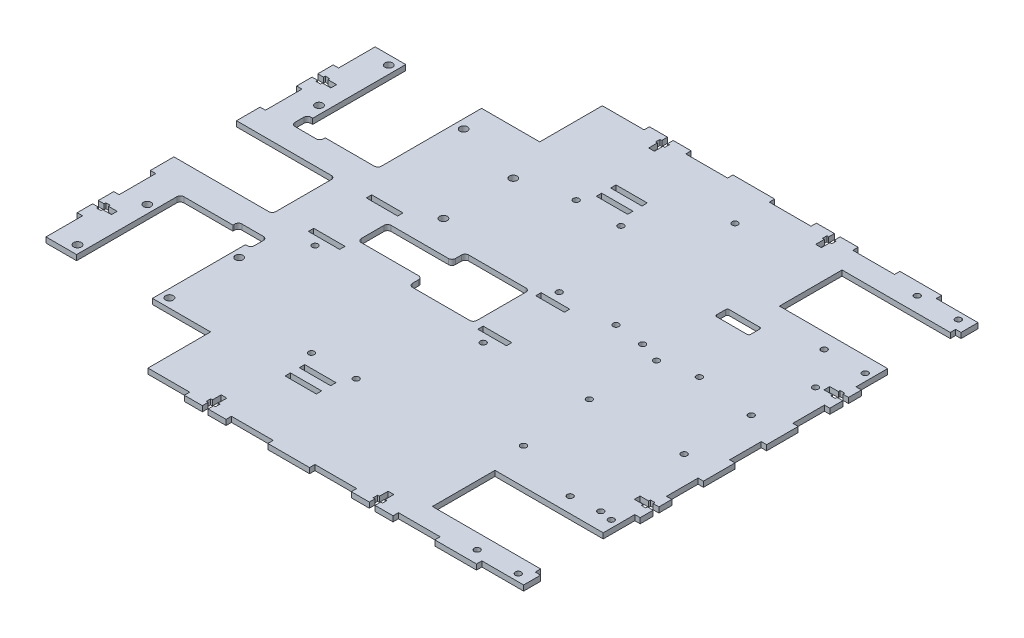
SolidWorks part; units mm, degrees
ref_plane "Front Plane" through (0, 0, 0) normal (0, 0, 1) x (1, 0, 0)
ref_plane "Top Plane" through (0, 0, 0) normal (0, 1, 0) x (1, 0, 0)
ref_plane "Right Plane" through (0, 0, 0) normal (1, 0, 0) x (0, 0, -1)
sketch "Sketch1" plane through (0, 0, 0) normal (0, 1, 0) x (1, 0, 0)
  line L0 (-152.5, 92) -> (-57.5, 92)
  line L5 (-57.5, 92) -> (-57.5, 130)
  line L6 (-57.5, 130) -> (152.5, 130)
  line L7 (152.5, 130) -> (152.5, -130)
  line L8 (152.5, -130) -> (-57.5, -130)
  line L9 (-57.5, -130) -> (-57.5, -92)
  line L10 (-57.5, -92) -> (-152.5, -92)
  line L11 (-152.5, -92) -> (-152.5, 92)
  line L12 (-152.5, 0) -> (152.5, 0) construction
  line L13 (134, -97) -> (134, 97) construction
  line L14 (89, 79.5) -> (152.5, 79.5)
  line L15 (89, 79.5) -> (89, 114.5)
  line L16 (89, 114.5) -> (152.5, 114.5)
  line L17 (152.5, 79.5) -> (152.5, 114.5)
  line L18 (89, 79.5) -> (152.5, 114.5) construction
  line L19 (89, 114.5) -> (152.5, 79.5) construction
  line L20 (89, -114.5) -> (152.5, -114.5)
  line L21 (89, -114.5) -> (89, -79.5)
  line L22 (89, -79.5) -> (152.5, -79.5)
  line L23 (152.5, -114.5) -> (152.5, -79.5)
  line L24 (89, -114.5) -> (152.5, -79.5) construction
  line L25 (89, -79.5) -> (152.5, -114.5) construction
  line L26 (145.5, 71) -> (122.5, 71) construction
  line L27 (145.5, 71) -> (145.5, 123) construction
  line L28 (145.5, 123) -> (122.5, 123) construction
  line L29 (122.5, 71) -> (122.5, 123) construction
  line L30 (145.5, 71) -> (122.5, 123) construction
  line L31 (145.5, 123) -> (122.5, 71) construction
  line L32 (122.5, -123) -> (145.5, -123) construction
  line L33 (122.5, -123) -> (122.5, -71) construction
  line L34 (122.5, -71) -> (145.5, -71) construction
  line L35 (145.5, -123) -> (145.5, -71) construction
  line L36 (122.5, -123) -> (145.5, -71) construction
  line L37 (122.5, -71) -> (145.5, -123) construction
  line L38 (-111.2, 92) -> (-111.2, -92) construction
  line L39 (-47.3096, 67) -> (-47.3096, 28) construction
  line L40 (-132.3981, -34) -> (-90.0019, -34)
  line L41 (-132.3981, -34) -> (-132.3981, -92)
  line L42 (-132.3981, -92) -> (-90.0019, -92)
  line L43 (-90.0019, -34) -> (-90.0019, -92)
  line L44 (-132.3981, -34) -> (-90.0019, -92) construction
  line L45 (-132.3981, -92) -> (-90.0019, -34) construction
  line L46 (-136.8906, -87) -> (-85.5093, -87) construction
  line L47 (-136.8906, -87) -> (-136.8906, -48) construction
  line L48 (-136.8906, -48) -> (-85.5093, -48) construction
  line L49 (-85.5093, -87) -> (-85.5093, -48) construction
  line L50 (-136.8906, -87) -> (-85.5093, -48) construction
  line L51 (-136.8906, -48) -> (-85.5093, -87) construction
  line L52 (-132.3981, 34) -> (-90.0019, 34)
  line L53 (-132.3981, 34) -> (-132.3981, 92)
  line L54 (-132.3981, 92) -> (-90.0019, 92)
  line L55 (-90.0019, 34) -> (-90.0019, 92)
  line L56 (-132.3981, 34) -> (-90.0019, 92) construction
  line L57 (-132.3981, 92) -> (-90.0019, 34) construction
  line L58 (-136.8906, 87) -> (-136.8906, 48) construction
  line L59 (-135.3981, 34) -> (-132.3981, 34) construction
  line L64 (-132.3981, 34) -> (-132.3981, 31) construction
  line L65 (-90.0019, -34) -> (-87.0019, -34) construction
  line L70 (-103.0019, -40) -> (-87.0019, -40)
  line L71 (-103.0019, -40) -> (-103.0019, -31)
  line L76 (-135.3981, 31) -> (-119.3981, 31)
  line L77 (-135.3981, 31) -> (-135.3981, 40)
  line L82 (-103.0019, -31) -> (-87.0019, -31)
  line L83 (-87.0019, -40) -> (-87.0019, -31)
  line L84 (-135.3981, 40) -> (-119.3981, 40)
  line L85 (-119.3981, 31) -> (-119.3981, 40)
  line L86 (-135.3981, 31) -> (-119.3981, 40) construction
  line L87 (-135.3981, 40) -> (-119.3981, 31) construction
  line L88 (-103.0019, -40) -> (-87.0019, -31) construction
  line L89 (-103.0019, -31) -> (-87.0019, -40) construction
  line L90 (-90.0019, -34) -> (-90.0019, -31) construction
  circle A0 centre (122.5, 123) radius 1.65
  circle A1 centre (145.5, 123) radius 1.65
  circle A2 centre (145.5, 71) radius 1.65
  circle A3 centre (122.5, 71) radius 1.65
  circle A4 centre (122.5, -71) radius 1.65
  circle A5 centre (145.5, -71) radius 1.65
  circle A6 centre (122.5, -123) radius 1.65
  circle A7 centre (145.5, -123) radius 1.65
  circle A8 centre (-136.8906, -48) radius 2.15
  circle A9 centre (-136.8906, -87) radius 2.15
  circle A10 centre (-85.5093, -87) radius 2.15
  circle A11 centre (-85.5093, -48) radius 2.15
  circle A12 centre (-136.8906, 87) radius 2.15
  circle A13 centre (-136.8906, 48) radius 2.15
  circle A14 centre (-85.0019, 77) radius 2.15
  circle A15 centre (-47.3096, 67) radius 2.15
  circle A16 centre (-47.3096, 28) radius 2.15
  point P5 (134, 97)
  point P8 (-152.5, 0)
  point P10 (152.5, 0)
  point P12 (0, 0)
  point P13 (120.75, 97)
  point P20 (120.75, -97)
  point P30 (134, -97)
  point P44 (134, 0)
  point P47 (-111.2, -63)
  point P52 (-111.2, -67.5)
  point P61 (-111.2, 63)
  point P76 (-95.0019, -35.5)
  point P96 (-127.3981, 35.5)
  dimension "D11" = 3.3
  dimension "D27" = 4.3
  dimension "D1" = 305
  dimension "D2" = 260
  dimension "D3" = 38
  dimension "D4" = 95
  dimension "D5" = 35
  dimension "D6" = 52
  dimension "D7" = 23
  dimension "D8" = 7
  dimension "D9" = 7
  dimension "D10" = 45
  dimension "D12" = 41.3
  dimension "D13" = 42.3962
  dimension "D14" = 51.3813
  dimension "D15" = 39
  dimension "D16" = 58
  dimension "D17" = 5
  dimension "D18" = 42.3962
  dimension "D19" = 21.1981
  dimension "D20" = 39
  dimension "D21" = 25.6906
  dimension "D22" = 63.8904
  dimension "D23" = 26.1981
  dimension "D24" = 5
  dimension "D25" = 15
  dimension "D26" = 25
  dimension "D28" = 16
  dimension "D29" = 3
  dimension "D30" = 9
  dimension "D31" = 3
  dimension "D32" = 3
extrude "Boss-Extrude1" add sketch "Sketch1" along normal blind 3 contours L21 L22 L7 L14 L15 L16 L6 L5 L0 L11 L10 L9 L8 L20 A7 A6 A5 A4 A3 A2 A1 A0
sketch "Sketch2" plane through (0, 3, 0) normal (0, 1, 0) x (1, 0, 0)
  line L0 (134, -97) -> (134, 97) construction
  line L1 (81, 18.75) -> (134, 18.75) construction
  line L2 (81, 18.75) -> (81, -18.75) construction
  line L3 (81, -18.75) -> (134, -18.75) construction
  line L4 (134, 18.75) -> (134, -18.75) construction
  line L5 (81, 18.75) -> (134, -18.75) construction
  line L6 (81, -18.75) -> (134, 18.75) construction
  line L9 (138.5, -23.5) -> (76.5, -23.5) construction
  line L10 (138.5, -23.5) -> (138.5, 23.5) construction
  line L11 (138.5, 23.5) -> (76.5, 23.5) construction
  line L12 (76.5, -23.5) -> (76.5, 23.5) construction
  line L13 (138.5, -23.5) -> (76.5, 23.5) construction
  line L14 (138.5, 23.5) -> (76.5, -23.5) construction
  circle A0 centre (81, 18.75) radius 1.65
  circle A1 centre (134, 18.75) radius 1.65
  circle A2 centre (134, -18.75) radius 1.65
  circle A3 centre (81, -18.75) radius 1.65
  point P0 (107.5, 0)
  point P12 (107.5, 0)
  dimension "D3" = 3.3
  dimension "D1" = 37.5
  dimension "D2" = 53
  dimension "D4" = 47
  dimension "D5" = 62
extrude "Cut-Extrude1" cut sketch "Sketch2" against normal through all both and the other way through all
sketch "Sketch3" plane through (0, 3, 0) normal (0, 1, 0) x (1, 0, 0)
  line L0 (64.76, 55.286) -> (143.5, 55.286) construction
  line L1 (143.5, 55.286) -> (143.5, -74) construction
  line L2 (143.5, -74) -> (71.491, -74) construction
  line L3 (71.491, -74) -> (64.76, -67.269) construction
  line L4 (64.76, -67.269) -> (64.76, 55.286) construction
  line L5 (69.205, 22.774) -> (100.955, 22.774) construction
  line L6 (85.08, -59.649) -> (85.08, 22.774) construction
  line L7 (138.42, 55.286) -> (138.42, 50.206) construction
  line L8 (138.42, 50.206) -> (143.5, 50.206) construction
  line L9 (143.5, -69.809) -> (138.42, -69.809) construction
  line L10 (138.42, -69.809) -> (138.42, -74) construction
  line L12 (152.5, 79.5) -> (152.5, -79.5) construction
  line L13 (76.64, 56.786) -> (93.64, 56.786)
  line L14 (75.64, 57.786) -> (75.64, 62.786)
  line L15 (76.64, 63.786) -> (93.64, 63.786)
  line L16 (94.64, 57.786) -> (94.64, 62.786)
  line L17 (75.64, 56.786) -> (94.64, 63.786) construction
  line L18 (75.64, 63.786) -> (94.64, 56.786) construction
  circle A0 centre (69.205, 22.774) radius 1.65
  circle A1 centre (100.955, 22.774) radius 1.65
  circle A2 centre (85.08, -59.649) radius 1.65
  circle A3 centre (138.42, 50.206) radius 1.65
  circle A4 centre (138.42, -69.809) radius 1.65
  arc A5 (76.64, 56.786) -> (75.64, 57.786) centre (76.64, 57.786) cw
  arc A6 (93.64, 56.786) -> (94.64, 57.786) centre (93.64, 57.786) ccw
  arc A7 (93.64, 63.786) -> (94.64, 62.786) centre (93.64, 62.786) cw
  arc A8 (75.64, 62.786) -> (76.64, 63.786) centre (76.64, 62.786) cw
  point P4 (85.14, 60.286)
  dimension "D5" = 3.3
  dimension "D18" = 1
  dimension "D1" = 78.74
  dimension "D2" = 129.286
  dimension "D3" = 135
  dimension "D4" = 6.731
  dimension "D6" = 31.75
  dimension "D7" = 82.423
  dimension "D8" = 32.512
  dimension "D9" = 4.445
  dimension "D10" = 5.08
  dimension "D11" = 4.191
  dimension "D12" = 74
  dimension "D13" = 9
  dimension "D14" = 19
  dimension "D15" = 7
  dimension "D16" = 1.5
  dimension "D17" = 20.38
extrude "Cut-Extrude2" cut sketch "Sketch3" against normal through all both and the other way through all
sketch "Sketch4" plane through (0, 3, 0) normal (0, 1, 0) x (1, 0, 0)
  line L0 (36.553, 107.122) -> (36.553, 24.699) construction
  line L1 (16.106, 121.473) -> (57, 121.473) construction
  line L2 (16.106, 121.473) -> (16.106, 20) construction
  line L3 (16.106, 20) -> (57, 20) construction
  line L4 (57, 121.473) -> (57, 20) construction
  line L5 (16.106, 121.473) -> (57, 20) construction
  line L6 (16.106, 20) -> (57, 121.473) construction
  line L7 (20.678, 24.699) -> (52.428, 24.699) construction
  line L8 (89, 79.5) -> (89, 114.5) construction
  line L9 (-57.5, 130) -> (152.5, 130) construction
  line L10 (-152.5, 0) -> (152.5, 0) construction
  line L11 (-152.5, -92) -> (-152.5, 92) construction
  line L12 (152.5, 79.5) -> (152.5, -79.5) construction
  circle A0 centre (20.678, 24.699) radius 1.65
  circle A1 centre (52.428, 24.699) radius 1.65
  circle A2 centre (36.553, 107.122) radius 1.65
  point P0 (36.553, 70.7365)
  point P9 (36.553, 24.699)
  dimension "D3" = 3.3
  dimension "D1" = 31.75
  dimension "D2" = 82.423
  dimension "D4" = 40.894
  dimension "D5" = 101.473
  dimension "D6" = 4.699
  dimension "D7" = 32
  dimension "D8" = 110
extrude "Cut-Extrude3" cut sketch "Sketch4" against normal through all both and the other way through all
sketch "Sketch6" plane through (0, 3, 0) normal (0, 1, 0) x (1, 0, 0)
  line L1 (-60.6174, -6.65) -> (-24.6174, -6.65)
  line L2 (-60.6174, -6.65) -> (-60.6174, 10.05)
  line L3 (-60.6174, 10.05) -> (-24.6174, 10.05)
  line L4 (-24.6174, -6.65) -> (-24.6174, 10.05)
  line L5 (-60.6174, -6.65) -> (-24.6174, 10.05) construction
  line L6 (-60.6174, 10.05) -> (-24.6174, -6.65) construction
  line L7 (11.3826, -14) -> (-24.6174, -14)
  line L8 (11.3826, -14) -> (11.3826, 17.4)
  line L9 (11.3826, 17.4) -> (-24.6174, 17.4)
  line L10 (-24.6174, -14) -> (-24.6174, 17.4)
  line L11 (11.3826, -14) -> (-24.6174, 17.4) construction
  line L12 (11.3826, 17.4) -> (-24.6174, -14) construction
  line L13 (-152.5, -92) -> (-152.5, 92) construction
  line L14 (-57.5, 130) -> (152.5, 130) construction
  point P0 (-42.6174, 1.7)
  point P5 (-6.6174, 1.7)
  dimension "D1" = 128.3
  dimension "D2" = 31.4
  dimension "D3" = 16.7
  dimension "D4" = 145.8826
  dimension "D5" = 36
  dimension "D6" = 36
extrude "Cut-Extrude5" cut sketch "Sketch6" against normal through all both and the other way through all contours L1 L4 L3 L2 | L10 L7 L8 L9 L4
fillet "Fillet1" radius 2 8 edges at (-60.6174, 1.5, 6.65) (-24.6174, 1.5, 6.65) (-24.6174, 1.5, 14) (11.3826, 1.5, 14) (11.3826, 1.5, -17.4) (-24.6174, 1.5, -17.4) (-24.6174, 1.5, -10.05) (-60.6174, 1.5, -10.05)
sketch "Sketch5" plane through (0, 3, 0) normal (0, 1, 0) x (1, 0, 0)
  line L0 (-152.5, -92) -> (-152.5, 92) construction
  line L1 (-152.5, 92) -> (-149.5, 92)
  line L2 (-152.5, 92) -> (-152.5, 71.5556)
  line L3 (-152.5, 71.5556) -> (-149.5, 71.5556)
  line L4 (-149.5, 92) -> (-149.5, 71.5556)
  line L5 (-152.5, 51.1111) -> (-149.5, 51.1111)
  line L6 (-152.5, 51.1111) -> (-152.5, 30.6667)
  line L7 (-152.5, 30.6667) -> (-149.5, 30.6667)
  line L8 (-149.5, 51.1111) -> (-149.5, 30.6667)
  line L9 (-132.3981, -92) -> (-152.5, -92) construction
  line L10 (-152.5, 10.2222) -> (-149.5, 10.2222)
  line L11 (-152.5, 10.2222) -> (-152.5, -10.2222)
  line L12 (-152.5, -10.2222) -> (-149.5, -10.2222)
  line L13 (-149.5, 10.2222) -> (-149.5, -10.2222)
  line L14 (-152.5, -30.6667) -> (-149.5, -30.6667)
  line L15 (-152.5, -30.6667) -> (-152.5, -51.1111)
  line L16 (-152.5, -51.1111) -> (-149.5, -51.1111)
  line L17 (-149.5, -30.6667) -> (-149.5, -51.1111)
  line L18 (-152.5, -71.5556) -> (-149.5, -71.5556)
  line L19 (-152.5, -71.5556) -> (-152.5, -92)
  line L20 (-152.5, -92) -> (-149.5, -92)
  line L21 (-149.5, -71.5556) -> (-149.5, -92)
  line L22 (-149.5, 71.5556) -> (-149.5, 51.1111) construction
  line L23 (-149.5, 30.6667) -> (-149.5, 10.2222) construction
  line L24 (-149.5, -10.2222) -> (-149.5, -30.6667) construction
  line L25 (-149.5, -51.1111) -> (-149.5, -71.5556) construction
  line L26 (152.5, 79.5) -> (152.5, -79.5) construction
  line L27 (152.5, 79.5) -> (149.5, 79.5)
  line L28 (152.5, 79.5) -> (152.5, 61.8333)
  line L29 (152.5, 61.8333) -> (149.5, 61.8333)
  line L30 (149.5, 79.5) -> (149.5, 61.8333)
  line L31 (152.5, 44.1667) -> (149.5, 44.1667)
  line L32 (152.5, 44.1667) -> (152.5, 26.5)
  line L33 (152.5, 26.5) -> (149.5, 26.5)
  line L34 (149.5, 44.1667) -> (149.5, 26.5)
  line L35 (149.5, 61.8333) -> (149.5, 44.1667) construction
  line L36 (152.5, 8.8333) -> (149.5, 8.8333)
  line L37 (152.5, 8.8333) -> (152.5, -8.8333)
  line L38 (152.5, -8.8333) -> (149.5, -8.8333)
  line L39 (149.5, 8.8333) -> (149.5, -8.8333)
  line L40 (152.5, -26.5) -> (149.5, -26.5)
  line L41 (152.5, -26.5) -> (152.5, -44.1667)
  line L42 (152.5, -44.1667) -> (149.5, -44.1667)
  line L43 (149.5, -26.5) -> (149.5, -44.1667)
  line L44 (152.5, -79.5) -> (149.5, -79.5)
  line L45 (152.5, -79.5) -> (152.5, -61.8333)
  line L46 (152.5, -61.8333) -> (149.5, -61.8333)
  line L47 (149.5, -79.5) -> (149.5, -61.8333)
  line L48 (149.5, 26.5) -> (149.5, 8.8333) construction
  line L49 (149.5, -8.8333) -> (149.5, -26.5) construction
  line L50 (149.5, -44.1667) -> (149.5, -61.8333) construction
  line L51 (-57.5, 130) -> (152.5, 130) construction
  line L52 (-57.5, 130) -> (-34.1667, 130)
  line L53 (-57.5, 130) -> (-57.5, 127)
  line L54 (-57.5, 127) -> (-34.1667, 127)
  line L55 (-34.1667, 130) -> (-34.1667, 127)
  line L56 (-10.8333, 130) -> (12.5, 130)
  line L57 (-10.8333, 130) -> (-10.8333, 127)
  line L58 (-10.8333, 127) -> (12.5, 127)
  line L59 (12.5, 130) -> (12.5, 127)
  line L60 (152.5, 130) -> (152.5, 114.5) construction
  line L61 (35.8333, 130) -> (59.1667, 130)
  line L62 (35.8333, 130) -> (35.8333, 127)
  line L63 (35.8333, 127) -> (59.1667, 127)
  line L64 (59.1667, 130) -> (59.1667, 127)
  line L65 (82.5, 130) -> (105.8333, 130)
  line L66 (82.5, 130) -> (82.5, 127)
  line L67 (82.5, 127) -> (105.8333, 127)
  line L68 (105.8333, 130) -> (105.8333, 127)
  line L69 (129.1667, 130) -> (152.5, 130)
  line L70 (129.1667, 130) -> (129.1667, 127)
  line L71 (129.1667, 127) -> (152.5, 127)
  line L72 (152.5, 130) -> (152.5, 127)
  line L73 (-34.1667, 127) -> (-10.8333, 127) construction
  line L74 (12.5, 127) -> (35.8333, 127) construction
  line L75 (59.1667, 127) -> (82.5, 127) construction
  line L76 (105.8333, 127) -> (129.1667, 127) construction
  line L77 (89, 114.5) -> (152.5, 114.5) construction
  line L78 (152.5, 117.5) -> (149.5, 117.5)
  line L79 (152.5, 117.5) -> (152.5, 114.5)
  line L80 (152.5, 114.5) -> (149.5, 114.5)
  line L81 (149.5, 117.5) -> (149.5, 114.5)
  line L82 (-1.65, 0) -> (1.65, 0) construction
  line L83 (105.8333, -127) -> (129.1667, -127) construction
  line L84 (59.1667, -127) -> (82.5, -127) construction
  line L85 (12.5, -127) -> (35.8333, -127) construction
  line L86 (-34.1667, -127) -> (-10.8333, -127) construction
  line L87 (149.5, -117.5) -> (149.5, -114.5)
  line L88 (152.5, -114.5) -> (149.5, -114.5)
  line L89 (152.5, -117.5) -> (152.5, -114.5)
  line L90 (152.5, -117.5) -> (149.5, -117.5)
  line L91 (152.5, -130) -> (152.5, -127)
  line L92 (129.1667, -127) -> (152.5, -127)
  line L93 (129.1667, -130) -> (129.1667, -127)
  line L94 (129.1667, -130) -> (152.5, -130)
  line L95 (105.8333, -130) -> (105.8333, -127)
  line L96 (82.5, -127) -> (105.8333, -127)
  line L97 (82.5, -130) -> (82.5, -127)
  line L98 (82.5, -130) -> (105.8333, -130)
  line L99 (59.1667, -130) -> (59.1667, -127)
  line L100 (35.8333, -127) -> (59.1667, -127)
  line L101 (35.8333, -130) -> (35.8333, -127)
  line L102 (35.8333, -130) -> (59.1667, -130)
  line L103 (12.5, -130) -> (12.5, -127)
  line L104 (-10.8333, -127) -> (12.5, -127)
  line L105 (-10.8333, -130) -> (-10.8333, -127)
  line L106 (-10.8333, -130) -> (12.5, -130)
  line L107 (-34.1667, -130) -> (-34.1667, -127)
  line L108 (-57.5, -127) -> (-34.1667, -127)
  line L109 (-57.5, -130) -> (-57.5, -127)
  line L110 (-57.5, -130) -> (-34.1667, -130)
  dimension "D1" = 3
extrude "Cut-Extrude4" cut sketch "Sketch5" against normal through all both and the other way through all
sketch "Sketch7" plane through (0, 3, 0) normal (0, 1, 0) x (1, 0, 0)
  line L0 (-152.5, 51.1111) -> (-152.5, 71.5556) construction
  line L1 (23.8826, -14.5) -> (23.8826, 17.9) construction
  line L2 (-19.1174, 74) -> (5.8826, 74) construction
  line L3 (-78.8412, -16) -> (-61.3412, -16)
  line L4 (-6.6174, 89.5) -> (-6.6174, 84.5) construction
  line L5 (-15.3571, -92.5) -> (2.1224, -92.5)
  line L6 (-15.3571, -92.5) -> (-15.3571, -89.5)
  line L7 (-15.3571, -89.5) -> (2.1224, -89.5)
  line L8 (2.1224, -92.5) -> (2.1224, -89.5)
  line L9 (-15.3571, -92.5) -> (2.1224, -89.5) construction
  line L10 (-15.3571, -89.5) -> (2.1224, -92.5) construction
  line L11 (-15.3571, -84.5) -> (2.1224, -84.5)
  line L12 (-15.3571, -84.5) -> (-15.3571, -81.5)
  line L13 (-15.3571, -81.5) -> (2.1224, -81.5)
  line L14 (2.1224, -84.5) -> (2.1224, -81.5)
  line L15 (-15.3571, -84.5) -> (2.1224, -81.5) construction
  line L16 (-15.3571, -81.5) -> (2.1224, -84.5) construction
  line L17 (-15.3571, 92.5) -> (2.1224, 92.5)
  line L18 (-15.3571, 92.5) -> (-15.3571, 89.5)
  line L19 (-15.3571, 89.5) -> (2.1224, 89.5)
  line L20 (2.1224, 92.5) -> (2.1224, 89.5)
  line L21 (-15.3571, 92.5) -> (2.1224, 89.5) construction
  line L22 (-15.3571, 89.5) -> (2.1224, 92.5) construction
  line L23 (-15.3571, 84.5) -> (2.1224, 84.5)
  line L24 (-15.3571, 84.5) -> (-15.3571, 81.5)
  line L25 (-15.3571, 81.5) -> (2.1224, 81.5)
  line L26 (2.1224, 84.5) -> (2.1224, 81.5)
  line L27 (-15.3571, 84.5) -> (2.1224, 81.5) construction
  line L28 (-15.3571, 81.5) -> (2.1224, 84.5) construction
  line L29 (-6.6174, -84.5) -> (-6.6174, -89.5) construction
  line L30 (-6.6174, 81.5) -> (-6.6174, -81.5) construction
  line L31 (-78.8412, -16) -> (-78.8412, -13)
  line L32 (-40.2293, -127) -> (-40.2293, 127) construction
  line L33 (-73.8412, -92) -> (-73.8412, 92) construction
  line L34 (-57.5, 127) -> (-34.1667, 127) construction
  line L35 (-78.8412, -13) -> (-61.3412, -13)
  line L36 (-61.3412, -16) -> (-61.3412, -13)
  line L37 (-90.0019, 92) -> (-57.5, 92) construction
  line L38 (-34.1667, -127) -> (-57.5, -127) construction
  line L39 (-57.5, -92) -> (-90.0019, -92) construction
  line L40 (-78.8412, -16) -> (-61.3412, -13) construction
  line L45 (-78.8412, -13) -> (-61.3412, -16) construction
  line L46 (-78.8412, 16.4) -> (-61.3412, 16.4)
  line L51 (-78.8412, 16.4) -> (-78.8412, 19.4)
  line L52 (-78.8412, 19.4) -> (-61.3412, 19.4)
  line L61 (-61.3412, 16.4) -> (-61.3412, 19.4)
  line L62 (-78.8412, 16.4) -> (-61.3412, 19.4) construction
  line L63 (-60.6174, 1.7) -> (11.3826, 1.7) construction
  line L64 (15.8826, -16) -> (31.8826, -16)
  line L65 (15.8826, -16) -> (15.8826, -13)
  line L66 (15.8826, -13) -> (31.8826, -13)
  line L67 (31.8826, -16) -> (31.8826, -13)
  line L68 (15.8826, -16) -> (31.8826, -13) construction
  line L69 (15.8826, -13) -> (31.8826, -16) construction
  line L70 (-60.6174, -4.65) -> (-60.6174, 8.05) construction
  line L71 (11.3826, -12) -> (11.3826, 15.4) construction
  line L84 (-19.1174, -74) -> (5.8826, -74) construction
  line L89 (-78.8412, 19.4) -> (-61.3412, 16.4) construction
  line L90 (-6.6174, -81.5) -> (-6.6174, -74) construction
  line L91 (15.8826, 16.4) -> (31.8826, 16.4)
  line L92 (15.8826, 16.4) -> (15.8826, 19.4)
  line L93 (15.8826, 19.4) -> (31.8826, 19.4)
  line L94 (31.8826, 16.4) -> (31.8826, 19.4)
  line L95 (15.8826, 16.4) -> (31.8826, 19.4) construction
  line L96 (15.8826, 19.4) -> (31.8826, 16.4) construction
  line L97 (-6.6174, 81.5) -> (-6.6174, 74) construction
  line L99 (-70.0912, -21) -> (-70.0912, -16) construction
  line L101 (23.8826, -21) -> (23.8826, -16) construction
  circle A0 centre (-19.1174, 74) radius 1.65
  circle A1 centre (5.8826, 74) radius 1.65
  circle A2 centre (-19.1174, -74) radius 1.65
  circle A3 centre (5.8826, -74) radius 1.65
  circle A4 centre (-70.0912, -21) radius 1.65
  circle A5 centre (23.8826, -21) radius 1.65
  point P2 (-6.6174, 0)
  point P3 (23.8826, 1.7)
  point P4 (-6.6174, -91)
  point P5 (-70.0912, -14.5)
  point P13 (-6.6174, -83)
  point P18 (-6.6174, 91)
  point P23 (-6.6174, 83)
  point P46 (-70.0912, 17.9)
  point P57 (23.8826, -14.5)
  point P73 (23.8826, 17.9)
  point P79 (-6.6174, 74)
  point P80 (-6.6174, -74)
  dimension "D14" = 3.3
  dimension "D1" = 145.8826
  dimension "D2" = 17.4795
  dimension "D3" = 3
  dimension "D4" = 5
  dimension "D5" = 163
  dimension "D6" = 33.6119
  dimension "D7" = 33.6119
  dimension "D8" = 22.5
  dimension "D9" = 3
  dimension "D10" = 17.5
  dimension "D11" = 77.2238
  dimension "D12" = 16
  dimension "D13" = 29.4
  dimension "D15" = 25
  dimension "D16" = 7.5
  dimension "D17" = 5
extrude "Cut-Extrude6" cut sketch "Sketch7" against normal through all both and the other way through all
sketch "Sketch8" plane through (0, 3, 0) normal (0, 1, 0) x (1, 0, 0)
  line L0 (-34.1667, 130) -> (-10.8333, 130) construction
  line L1 (-24.1, 119.5) -> (-20.9, 119.5)
  line L2 (-24.1, 119.5) -> (-24.1, 130)
  line L3 (-24.1, 130) -> (-20.9, 130)
  line L4 (-20.9, 119.5) -> (-20.9, 130)
  line L5 (-24.1, 119.5) -> (-20.9, 130) construction
  line L6 (-24.1, 130) -> (-20.9, 119.5) construction
  line L7 (59.1667, 130) -> (82.5, 130) construction
  line L8 (69.2333, 119.5) -> (72.4333, 119.5)
  line L9 (69.2333, 119.5) -> (69.2333, 130)
  line L10 (69.2333, 130) -> (72.4333, 130)
  line L11 (72.4333, 119.5) -> (72.4333, 130)
  line L12 (69.2333, 119.5) -> (72.4333, 130) construction
  line L13 (69.2333, 130) -> (72.4333, 119.5) construction
  line L14 (82.5, -130) -> (59.1667, -130) construction
  line L15 (72.4333, -119.5) -> (69.2333, -119.5)
  line L16 (72.4333, -119.5) -> (72.4333, -130)
  line L17 (72.4333, -130) -> (69.2333, -130)
  line L18 (69.2333, -119.5) -> (69.2333, -130)
  line L19 (72.4333, -119.5) -> (69.2333, -130) construction
  line L20 (72.4333, -130) -> (69.2333, -119.5) construction
  line L21 (-10.8333, -130) -> (-34.1667, -130) construction
  line L22 (-24.1, -119.5) -> (-20.9, -119.5)
  line L23 (-24.1, -119.5) -> (-24.1, -130)
  line L24 (-24.1, -130) -> (-20.9, -130)
  line L25 (-20.9, -119.5) -> (-20.9, -130)
  line L26 (-24.1, -119.5) -> (-20.9, -130) construction
  line L27 (-24.1, -130) -> (-20.9, -119.5) construction
  line L28 (152.5, 61.8333) -> (152.5, 44.1667) construction
  line L29 (142, 54.6) -> (152.5, 54.6)
  line L30 (142, 54.6) -> (142, 51.4)
  line L31 (142, 51.4) -> (152.5, 51.4)
  line L32 (152.5, 54.6) -> (152.5, 51.4)
  line L33 (142, 54.6) -> (152.5, 51.4) construction
  line L34 (142, 51.4) -> (152.5, 54.6) construction
  line L35 (152.5, -44.1667) -> (152.5, -61.8333) construction
  line L36 (142, -51.4) -> (152.5, -51.4)
  line L37 (142, -51.4) -> (142, -54.6)
  line L38 (142, -54.6) -> (152.5, -54.6)
  line L39 (152.5, -51.4) -> (152.5, -54.6)
  line L40 (142, -51.4) -> (152.5, -54.6) construction
  line L41 (142, -54.6) -> (152.5, -51.4) construction
  line L42 (-152.5, 51.1111) -> (-152.5, 71.5556) construction
  line L43 (-142, 59.7333) -> (-152.5, 59.7333)
  line L44 (-142, 59.7333) -> (-142, 62.9333)
  line L45 (-142, 62.9333) -> (-152.5, 62.9333)
  line L46 (-152.5, 59.7333) -> (-152.5, 62.9333)
  line L47 (-142, 59.7333) -> (-152.5, 62.9333) construction
  line L48 (-142, 62.9333) -> (-152.5, 59.7333) construction
  line L49 (-152.5, -71.5556) -> (-152.5, -51.1111) construction
  line L50 (-142, -62.9333) -> (-152.5, -62.9333)
  line L51 (-142, -62.9333) -> (-142, -59.7333)
  line L52 (-142, -59.7333) -> (-152.5, -59.7333)
  line L53 (-152.5, -62.9333) -> (-152.5, -59.7333)
  line L54 (-142, -62.9333) -> (-152.5, -59.7333) construction
  line L55 (-142, -59.7333) -> (-152.5, -62.9333) construction
  line L56 (-22.5, 125.575) -> (-22.5, 130) construction
  line L57 (-25.1, 124.325) -> (-19.9, 124.325)
  line L58 (-25.1, 124.325) -> (-25.1, 126.825)
  line L59 (-25.1, 126.825) -> (-19.9, 126.825)
  line L60 (-19.9, 124.325) -> (-19.9, 126.825)
  line L61 (-25.1, 124.325) -> (-19.9, 126.825) construction
  line L62 (-25.1, 126.825) -> (-19.9, 124.325) construction
  line L63 (68.2333, 126.825) -> (73.4333, 126.825)
  line L64 (68.2333, 126.825) -> (68.2333, 124.325)
  line L65 (68.2333, 124.325) -> (73.4333, 124.325)
  line L66 (73.4333, 126.825) -> (73.4333, 124.325)
  line L67 (68.2333, 126.825) -> (73.4333, 124.325) construction
  line L68 (68.2333, 124.325) -> (73.4333, 126.825) construction
  line L69 (149.325, 50.4) -> (146.825, 50.4)
  line L70 (149.325, 50.4) -> (149.325, 55.6)
  line L71 (149.325, 55.6) -> (146.825, 55.6)
  line L72 (146.825, 50.4) -> (146.825, 55.6)
  line L73 (149.325, 50.4) -> (146.825, 55.6) construction
  line L74 (149.325, 55.6) -> (146.825, 50.4) construction
  line L75 (149.325, -55.6) -> (146.825, -55.6)
  line L76 (149.325, -55.6) -> (149.325, -50.4)
  line L77 (149.325, -50.4) -> (146.825, -50.4)
  line L78 (146.825, -55.6) -> (146.825, -50.4)
  line L79 (149.325, -55.6) -> (146.825, -50.4) construction
  line L80 (149.325, -50.4) -> (146.825, -55.6) construction
  line L81 (68.2333, -126.825) -> (73.4333, -126.825)
  line L82 (68.2333, -126.825) -> (68.2333, -124.325)
  line L83 (68.2333, -124.325) -> (73.4333, -124.325)
  line L84 (73.4333, -126.825) -> (73.4333, -124.325)
  line L85 (68.2333, -126.825) -> (73.4333, -124.325) construction
  line L86 (68.2333, -124.325) -> (73.4333, -126.825) construction
  line L87 (-25.1, -126.825) -> (-19.9, -126.825)
  line L88 (-25.1, -126.825) -> (-25.1, -124.325)
  line L89 (-25.1, -124.325) -> (-19.9, -124.325)
  line L90 (-19.9, -126.825) -> (-19.9, -124.325)
  line L91 (-25.1, -126.825) -> (-19.9, -124.325) construction
  line L92 (-25.1, -124.325) -> (-19.9, -126.825) construction
  line L93 (-149.325, -58.7333) -> (-146.825, -58.7333)
  line L94 (-149.325, -58.7333) -> (-149.325, -63.9333)
  line L95 (-149.325, -63.9333) -> (-146.825, -63.9333)
  line L96 (-146.825, -58.7333) -> (-146.825, -63.9333)
  line L97 (-149.325, -58.7333) -> (-146.825, -63.9333) construction
  line L98 (-149.325, -63.9333) -> (-146.825, -58.7333) construction
  line L99 (-149.325, 63.9333) -> (-146.825, 63.9333)
  line L100 (-149.325, 63.9333) -> (-149.325, 58.7333)
  line L101 (-149.325, 58.7333) -> (-146.825, 58.7333)
  line L102 (-146.825, 63.9333) -> (-146.825, 58.7333)
  line L103 (-149.325, 63.9333) -> (-146.825, 58.7333) construction
  line L104 (-149.325, 58.7333) -> (-146.825, 63.9333) construction
  line L105 (70.8333, 125.575) -> (70.8333, 130) construction
  line L106 (148.075, 53) -> (152.5, 53) construction
  line L107 (152.5, -53) -> (148.075, -53) construction
  line L108 (70.8333, -130) -> (70.8333, -125.575) construction
  line L109 (-22.5, -130) -> (-22.5, -125.575) construction
  line L110 (-152.5, -61.3333) -> (-148.075, -61.3333) construction
  line L111 (-152.5, 61.3333) -> (-148.075, 61.3333) construction
  point P0 (-22.5, 124.75)
  point P7 (70.8333, 124.75)
  point P14 (70.8333, -124.75)
  point P21 (-22.5, -124.75)
  point P28 (147.25, 53)
  point P35 (147.25, -53)
  point P42 (-147.25, 61.3333)
  point P49 (-147.25, -61.3333)
  point P56 (-22.5, -125.575)
  point P57 (-152.5, 61.3333)
  point P58 (-152.5, -61.3333)
  point P59 (-22.5, -130)
  point P60 (70.8333, -130)
  point P61 (-22.5, 130)
  point P62 (70.8333, 130)
  point P63 (152.5, 53)
  point P64 (152.5, -53)
  point P65 (-22.5, 125.575)
  point P70 (70.8333, 125.575)
  point P75 (148.075, 53)
  point P80 (148.075, -53)
  point P85 (70.8333, -125.575)
  point P94 (-148.075, -61.3333)
  point P99 (-148.075, 61.3333)
  dimension "D1" = 10.5
  dimension "D2" = 3.2
  dimension "D3" = 2.5
  dimension "D4" = 5.2
  dimension "D5" = 3.175
extrude "Cut-Extrude7" cut sketch "Sketch8" against normal through all both and the other way through all contours L45 L102 L43 L44 | L96 L52 L94 L50 | L100 L45 L46 L43 | L102 L99 L100 L45 | L102 L43 L100 L101 | L102 L45 L100 L43 | L57 L2 L1 L4 | L59 L58 L57 L2 | L2 L59 L4 L3 | L9 L10 L11 L8 | L63 L66 L65 L64 | L29 L32 L31 L30 | L71 L72 L69 L70 | L38 L39 L36 L37 | L78 L77 L76 L75 | L18 L17 L16 L15 | L83 L84 L81 L82 | L23 L24 L25 L22 | L89 L90 L87 L88
sketch "Sketch9" plane through (0, 3, 0) normal (0, 1, 0) x (1, 0, 0)
  line L0 (-152.5, 10.2222) -> (-152.5, 30.6667) construction
  line L1 (-152.5, -17.5) -> (-97.5, -17.5)
  line L2 (-152.5, -17.5) -> (-152.5, 17.5)
  line L3 (-152.5, 17.5) -> (-97.5, 17.5)
  line L4 (-97.5, -17.5) -> (-97.5, 17.5)
  line L5 (-152.5, -17.5) -> (-97.5, 17.5) construction
  line L6 (-152.5, 17.5) -> (-97.5, -17.5) construction
  point P0 (-125, 0)
  point P5 (0, 0)
  dimension "D1" = 35
  dimension "D2" = 55
extrude "Cut-Extrude8" cut sketch "Sketch9" against normal through all both and the other way through all
fillet "Fillet2" radius 2 10 edges at (-97.5, 1.5, 17.5) (-97.5, 1.5, -17.5) (-135.3981, 1.5, -40) (-119.3981, 1.5, -31) (-135.3981, 1.5, -31) (-132.3981, 1.5, 34) (-103.0019, 1.5, 31) (-87.0019, 1.5, 40) (-87.0019, 1.5, 31) (-90.0019, 1.5, -34)
